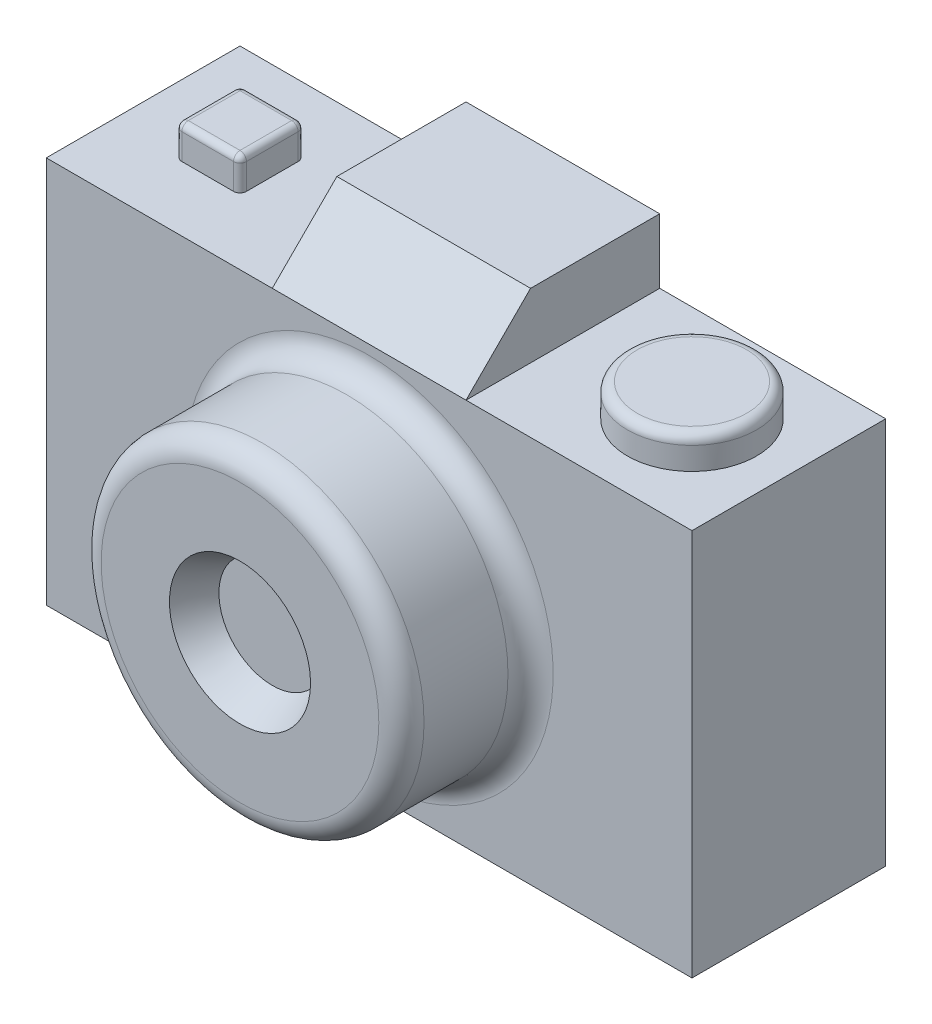
SolidWorks part; units mm, degrees
ref_plane "Front Plane" through (0, 0, 0) normal (0, 0, 1) x (1, 0, 0)
ref_plane "Top Plane" through (0, 0, 0) normal (0, 1, 0) x (1, 0, 0)
ref_plane "Right Plane" through (0, 0, 0) normal (1, 0, 0) x (0, 0, -1)
sketch "Sketch1" plane through (0, 0, 0) normal (0, 1, 0) x (1, 0, 0)
  line L1 (0, 0) -> (100, 0)
  line L2 (0, 0) -> (0, 30)
  line L3 (0, 30) -> (100, 30)
  line L4 (100, 0) -> (100, 30)
  dimension "D1" = 100
  dimension "D2" = 30
extrude "Boss-Extrude1" add sketch "Sketch1" along normal blind 60
sketch "Sketch2" plane through (0, 0, 0) normal (0, 0, 1) x (1, 0, 0)
  line L0 (0, 60) -> (100, 0) construction
  circle A0 centre (50, 30) radius 25
  point P10 (-37.5228, 55.9244)
  dimension "D1" = 50
extrude "Boss-Extrude2" add sketch "Sketch2" along normal blind 20
sketch "Sketch3" plane through (0, 60, 0) normal (0, 1, 0) x (1, 0, 0)
  line L0 (0, 15) -> (100, 15) construction
  line L1 (0, 30) -> (0, 0) construction
  line L2 (100, 0) -> (100, 30) construction
  line L4 (10, 20) -> (20, 20)
  line L5 (10, 20) -> (10, 10)
  line L6 (10, 10) -> (20, 10)
  line L7 (20, 20) -> (20, 10)
  line L8 (10, 20) -> (20, 10) construction
  line L9 (10, 10) -> (20, 20) construction
  circle A0 centre (85, 15) radius 10
  point P8 (15, 15)
  dimension "D2" = 20
  dimension "D1" = 10
  dimension "D3" = 15
  dimension "D4" = 15
extrude "Boss-Extrude3" add sketch "Sketch3" along normal blind 5
sketch "Sketch4" plane through (0, 60, 0) normal (0, 1, 0) x (1, 0, 0)
  line L0 (100, 30) -> (0, 30) construction
  line L1 (35, 30) -> (65, 30)
  line L2 (35, 30) -> (35, 0)
  line L3 (35, 0) -> (65, 0)
  line L4 (65, 30) -> (65, 0)
  line L5 (0, 0) -> (100, 0) construction
  line L6 (100, 0) -> (100, 30) construction
  dimension "D1" = 30
  dimension "D2" = 35
extrude "Boss-Extrude4" add sketch "Sketch4" along normal blind 10
chamfer "Chamfer1" distance 10 angle 45 1 edges at (50, 70, 0)
fillet "Fillet1" radius 1 8 edges at (10, 62.5, -20) (20, 62.5, -20) (20, 62.5, -10) (10, 62.5, -10) (15, 65, -10) (10, 65, -15) (15, 65, -20) (20, 65, -15)
fillet "Fillet2" radius 1.5 1 edges at (85, 65, -5)
fillet "Fillet3" radius 3.5 2 edges at (75, 30, 0) (75, 30, 20)
sketch "Sketch5" plane through (0, 0, 20) normal (0, 0, 1) x (1, 0, 0)
  circle A0 centre (50, 30) radius 10.9251
extrude "Cut-Extrude1" cut sketch "Sketch5" against normal blind 5 draft 28
